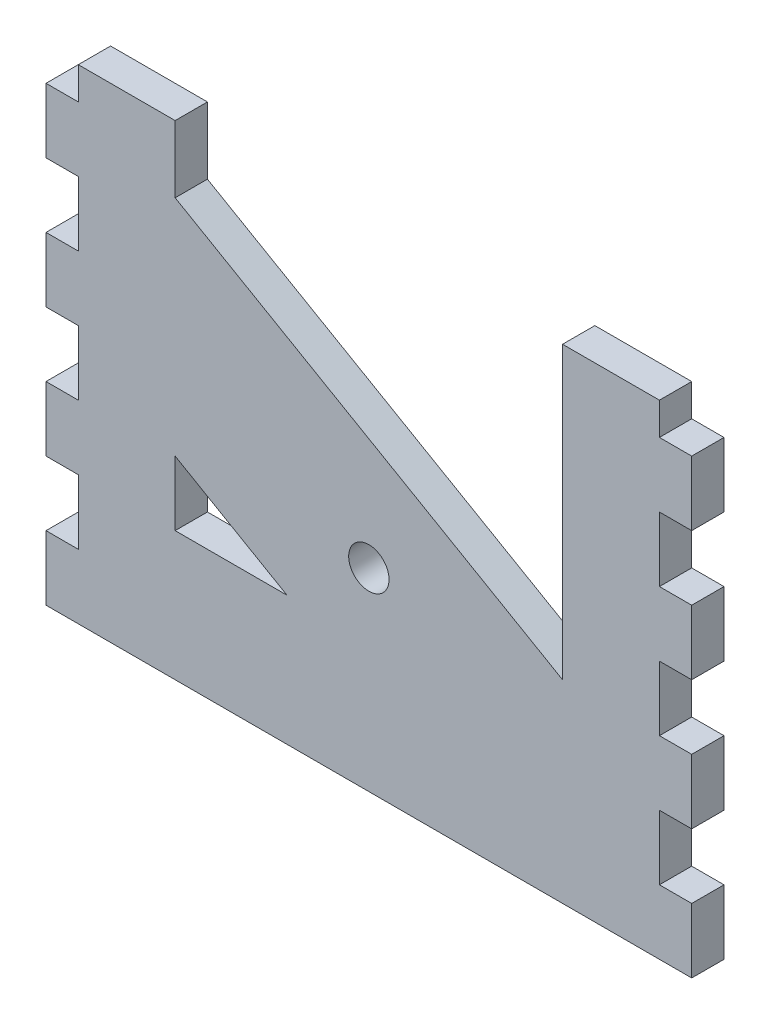
SolidWorks part; units mm, degrees
material "Pine"
ref_plane "Front Plane" through (0, 0, 0) normal (0, 0, 1) x (1, 0, 0)
ref_plane "Top Plane" through (0, 0, 0) normal (0, 1, 0) x (1, 0, 0)
ref_plane "Right Plane" through (0, 0, 0) normal (1, 0, 0) x (0, 0, -1)
sketch "Sketch1" plane through (0, 0, 0) normal (0, 0, 1) x (1, 0, 0)
  line L1 (0, 0) -> (127, 0)
  line L2 (0, 0) -> (0, 95.25)
  line L3 (0, 95.25) -> (127, 95.25)
  line L4 (127, 0) -> (127, 95.25)
  dimension "D1" = 127
  dimension "D2" = 95.25
extrude "Boss-Extrude1" add sketch "Sketch1" along normal blind 6.35
sketch "Sketch2" plane through (0, 0, 6.35) normal (0, 0, 1) x (1, 0, 0)
  line L0 (0, 95.25) -> (0, 0) construction
  line L1 (0, 0) -> (127, 0) construction
  circle A0 centre (63.5, 38.1) radius 3.9687
  dimension "D3" = 7.9375
  dimension "D1" = 63.5
  dimension "D2" = 38.1
extrude "Cut-Extrude1" cut sketch "Sketch2" against normal through all
sketch "Sketch3" plane through (0, 0, 6.35) normal (0, 0, 1) x (1, 0, 0)
  line L0 (0, 95.25) -> (0, 0) construction
  line L1 (0, 12.7) -> (6.35, 12.7)
  line L2 (0, 12.7) -> (0, 25.4)
  line L3 (0, 25.4) -> (6.35, 25.4)
  line L4 (6.35, 12.7) -> (6.35, 25.4)
  dimension "D1" = 6.35
  dimension "D2" = 12.7
  dimension "D3" = 12.7
extrude "Cut-Extrude2" cut sketch "Sketch3" against normal through all
sketch "Sketch4" plane through (0, 0, 6.35) normal (0, 0, 1) x (1, 0, 0)
  line L0 (127, 0) -> (127, 95.25) construction
  line L1 (127, 12.7) -> (120.65, 12.7)
  line L2 (127, 12.7) -> (127, 25.4)
  line L3 (127, 25.4) -> (120.65, 25.4)
  line L4 (120.65, 12.7) -> (120.65, 25.4)
  line L5 (6.35, 12.7) -> (6.35, 25.4) construction
  line L6 (0, 12.7) -> (6.35, 12.7) construction
extrude "Cut-Extrude3" cut sketch "Sketch4" against normal through all
pattern_linear "LPattern1" count 4 spacing 25.4 along (0, 1, 0) of "Cut-Extrude2", "Cut-Extrude3"
sketch "Sketch5" plane through (0, 0, 6.35) normal (0, 0, 1) x (1, 0, 0)
  line L0 (25.4, 95.25) -> (25.4, 82.0941)
  line L1 (120.65, 95.25) -> (6.35, 95.25) construction
  line L2 (25.4, 82.0941) -> (101.6, 38.1)
  line L3 (101.6, 38.1) -> (101.6, 95.25)
  line L4 (101.6, 95.25) -> (25.4, 95.25)
  line L5 (6.35, 88.9) -> (6.35, 95.25) construction
  line L6 (120.65, 76.2) -> (120.65, 63.5) construction
  line L7 (25.4, 38.1) -> (47.397, 25.4)
  line L8 (47.397, 25.4) -> (25.4, 25.4)
  line L9 (25.4, 25.4) -> (25.4, 38.1)
  line L11 (0, 0) -> (127, 0) construction
  circle A0 centre (63.5, 38.1) radius 3.9687 construction
  dimension "D2" = 19.05
  dimension "D5" = 19.05
  dimension "D1" = 19.05
  dimension "D3" = 120
  dimension "D4" = 19.05
  dimension "D6" = 25.4
extrude "Cut-Extrude4" cut sketch "Sketch5" against normal through all
